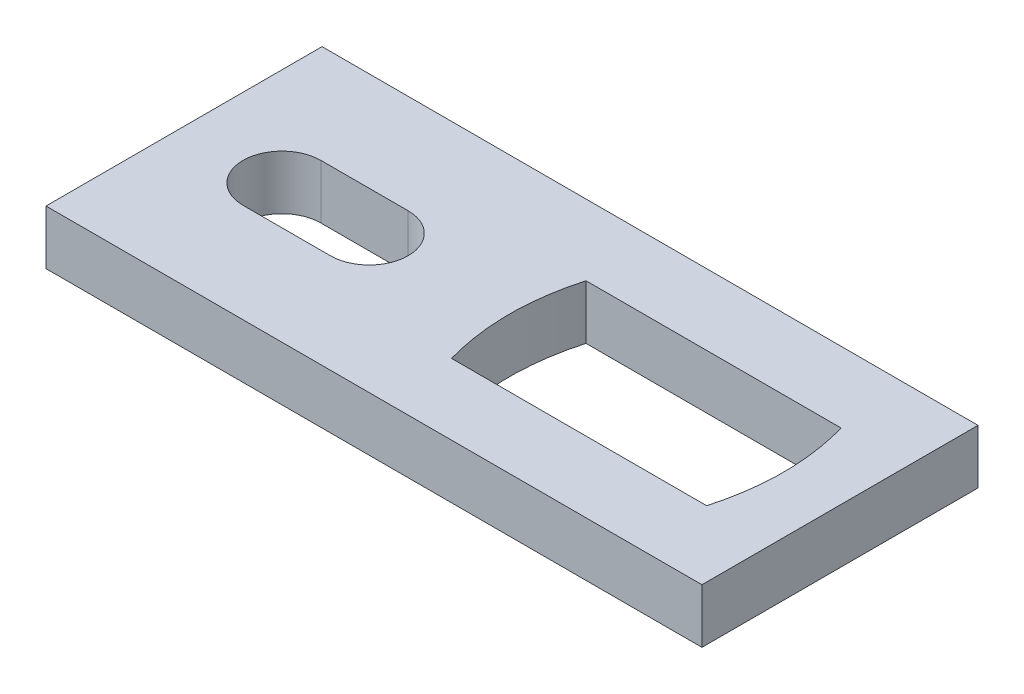
SolidWorks part; units mm, degrees
ref_plane "Front Plane" through (0, 0, 0) normal (0, 0, 1) x (1, 0, 0)
ref_plane "Top Plane" through (0, 0, 0) normal (0, 1, 0) x (1, 0, 0)
ref_plane "Right Plane" through (0, 0, 0) normal (1, 0, 0) x (0, 0, -1)
sketch "Sketch1" plane through (0, 0, 0) normal (0, 1, 0) x (1, 0, 0)
  line L0 (-35.306, 14.859) -> (35.306, -14.859) construction
  line L1 (-35.306, -14.859) -> (35.306, -14.859)
  line L2 (-35.306, -14.859) -> (-35.306, 14.859)
  line L3 (-35.306, 14.859) -> (35.306, 14.859)
  line L4 (35.306, -14.859) -> (35.306, 14.859)
  line L5 (-35.306, -14.859) -> (35.306, 14.859) construction
  point P4 (0, 0)
  dimension "D1" = 70.612
  dimension "D2" = 29.718
extrude "Boss-Extrude1" add sketch "Sketch1" along normal blind 5.842
sketch "Sketch2" plane through (0, 5.842, 0) normal (0, 1, 0) x (1, 0, 0)
  line L0 (-35.306, -14.859) -> (35.306, -14.859) construction
  line L1 (0.7278, 7.239) -> (28.194, 7.239)
  line L3 (0.7278, -7.239) -> (28.194, -7.239)
  line L5 (35.306, 14.859) -> (-35.306, 14.859) construction
  line L6 (35.306, -14.859) -> (35.306, 14.859) construction
  line L7 (14.4609, 7.239) -> (14.4609, -7.239) construction
  spline S0 degree 2 poles (28.194, -7.239) (30.226, 0) (28.194, 7.239) knots 0 0 0 1 1 1
  spline S1 degree 2 poles (0.7278, -7.239) (-1.3042, 0) (0.7278, 7.239) knots 0 0 0 1 1 1
  dimension "D1" = 7.62
  dimension "D2" = 7.62
  dimension "D4" = 7.112
  dimension "D5" = 7.112
extrude "Cut-Extrude1" cut sketch "Sketch2" against normal through all
sketch "Sketch3" plane through (0, 0, 0) normal (0, -1, 0) x (1, 0, 0)
  line L0 (-28.956, 0) -> (-35.306, 0) construction
  line L1 (-24.765, 4.191) -> (-15.367, 4.191)
  line L3 (-24.765, -4.191) -> (-15.367, -4.191)
  line L5 (-35.306, -14.859) -> (-35.306, 14.859) construction
  arc A0 (-15.367, -4.191) -> (-15.367, 4.191) centre (-15.367, 0) ccw
  arc A1 (-24.765, 4.191) -> (-24.765, -4.191) centre (-24.765, 0) ccw
  point P1 (-11.176, 0)
  point P3 (-28.956, 0)
  dimension "D1" = 17.78
  dimension "D2" = 8.382
  dimension "D3" = 6.35
extrude "Cut-Extrude2" cut sketch "Sketch3" against normal through all
